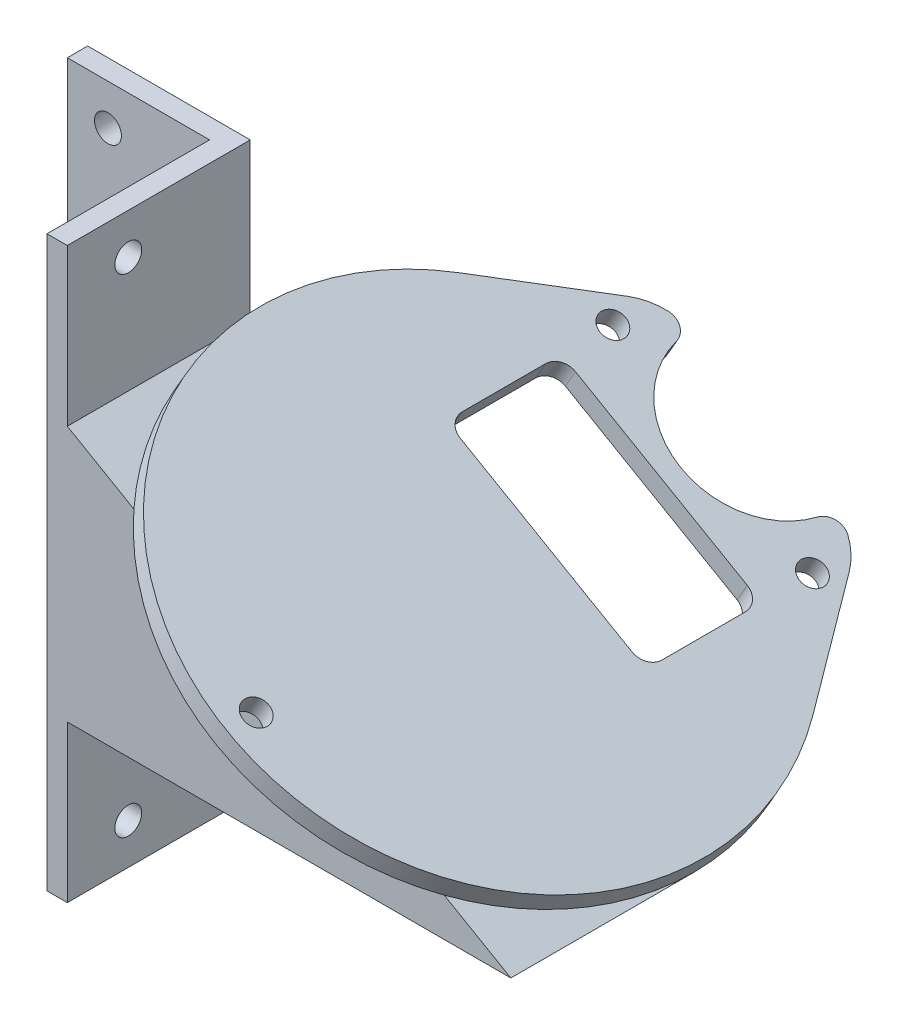
SolidWorks part; units mm, degrees
ref_plane "Front Plane" through (0, 0, 0) normal (0, 0, 1) x (1, 0, 0)
ref_plane "Top Plane" through (0, 0, 0) normal (0, 1, 0) x (1, 0, 0)
ref_plane "Right Plane" through (0, 0, 0) normal (1, 0, 0) x (0, 0, -1)
sketch "Sketch2" plane through (0, 0, 0) normal (1, 0, 0) x (0, 0, -1)
  line L0 (0, 0) -> (26.9799, 0) construction
ref_plane "Plane1" through (0, 0, 0) normal (0.5, 0.866, 0) x (0, 0, -1)
sketch "Sketch3" plane through (0, 0, 0) normal (0.5, 0.866, 0) x (0, 0, -1)
  line L0 (36, 18) -> (36, -18) construction
  line L1 (-200000, 0) -> (200026.9799, 0) construction
  line L2 (24, 32) -> (40, 20)
  line L3 (44, 12) -> (44, -12) construction
  line L4 (40, -20) -> (24, -32)
  line L6 (10, 18) -> (28, 18)
  line L7 (10, 18) -> (10, -18)
  line L8 (10, -18) -> (28, -18)
  line L9 (28, 18) -> (28, -18)
  circle A0 centre (0, 0) radius 29.91 construction
  circle A1 centre (-35.3, 0) radius 2
  circle A2 centre (36, 18) radius 2
  circle A3 centre (36, -18) radius 2
  circle A4 centre (44, 0) radius 13 construction
  arc A5 (24, 32) -> (24, -32) centre (0, 0) ccw
  arc A6 (44, -12) -> (40, -20) centre (34, -12) cw
  arc A7 (40, 20) -> (44, 12) centre (34, 12) cw
  circle A8 centre (44, 0) radius 13
  point P9 (36, 0)
  point P10 (44, 0)
  point P25 (44, 17)
  point P29 (10, 0)
  point P30 (10, 0)
  point P31 (0, -40)
  dimension "D1" = 59.82
  dimension "D2" = 4
  dimension "D7" = 26
  dimension "D8" = 40
  dimension "D10" = 10
  dimension "D3" = 35.3
  dimension "D4" = 36
  dimension "D5" = 36
  dimension "D6" = 44
  dimension "D9" = 25
  dimension "D11" = 10
  dimension "D12" = 18
  dimension "D13" = 36
extrude "Boss-Extrude1" add sketch "Sketch3" along normal blind 3.175 contours A8 A7 L2 A5 L4 A6 L6 L9 L8 L7 A1 A2 A3
fillet "Fillet1" radius 2.5 6 edges at (16.3822, -7.6252, -10) (16.3822, -7.6252, -28) (-14.7947, 10.3748, -28) (-14.7947, 10.3748, -10) (-10.4645, 7.8748, -43.9499) (12.052, -5.1251, -43.9499)
ref_plane "Plane2" through (0, -20, 0) normal (0, 1, 0) x (1, 0, 0)
sketch "Sketch4" plane through (0, -20, 0) normal (0, 1, 0) x (1, 0, 0)
  line L0 (18.766, 44.45) -> (18.766, -44.45) construction
  line L1 (34.641, 44.45) -> (2.891, 44.45)
  line L2 (34.641, 44.45) -> (34.641, -44.45)
  line L3 (34.641, -44.45) -> (2.891, -44.45)
  line L4 (2.891, 44.45) -> (2.891, -44.45)
  line L5 (18.766, 38.1) -> (18.766, -38.1) construction
  circle A0 centre (18.766, 38.1) radius 2.25
  circle A1 centre (18.766, -38.1) radius 2.25
  dimension "D2" = 4.5
  dimension "D1" = 31.75
  dimension "D3" = 76.2
  dimension "D4" = 38.1
  dimension "D5" = 88.9
sketch "Sketch6" plane through (0, 0, 0) normal (0, 0, 1) x (1, 0, 0)
  line L1 (-34.641, 44.45) -> (-60.041, 44.45)
  line L2 (-34.641, 44.45) -> (-34.641, -44.45)
  line L3 (-34.641, -44.45) -> (-60.041, -44.45)
  line L4 (-60.041, 44.45) -> (-60.041, -44.45)
  line L15 (-34.641, 20) -> (34.641, -20) construction
  line L16 (15.5885, -9) -> (-34.641, -9)
  line L17 (-34.641, 20) -> (34.641, -20)
  line L18 (0, 0) -> (-34.641, 0) construction
  point P5 (0, 0)
  point P6 (0, 0)
  dimension "D1" = 88.9
  dimension "D2" = 25.4
extrude "Boss-Extrude2" add sketch "Sketch6" along normal blind 3.175 contours L18 L17 L2
sketch "Sketch7" plane through (0, 0, 0) normal (0, 0, -1) x (-1, 0, 0)
  line L1 (34.641, -44.45) -> (37.816, -44.45)
  line L2 (34.641, -44.45) -> (34.641, 44.45)
  line L3 (34.641, 44.45) -> (37.816, 44.45)
  line L4 (37.816, -44.45) -> (37.816, 44.45)
  line L5 (34.641, 44.45) -> (60.041, 44.45) construction
  point P5 (37.816, 44.45)
  point P7 (0, 0)
  point P8 (0, 0)
  point P10 (0, 0)
  point P11 (0, 0)
  point P12 (34.641, -44.45)
  dimension "D1" = 3.175
extrude "Boss-Extrude3" add sketch "Sketch7" against normal blind 28.575
sketch "Sketch8" plane through (0, 0, 3.175) normal (0, 0, 1) x (1, 0, 0)
  line L0 (-37.816, -44.45) -> (-37.816, 44.45) construction
  line L4 (-37.816, 44.45) -> (-60.041, 44.45) construction
  circle A0 centre (-53.691, 38.1) radius 2.1
  circle A1 centre (-53.691, -38.1) radius 2.1
  point P6 (0, 0)
  point P7 (0, 0)
  dimension "D2" = 4.2
  dimension "D1" = 15.875
  dimension "D3" = 76.2
  dimension "D4" = 6.35
extrude "Cut-Extrude1" cut sketch "Sketch8" against normal blind 25.4
sketch "Sketch9" plane through (-37.816, 0, 0) normal (-1, 0, 0) x (0, 0, 1)
  line L0 (3.175, 36) -> (3.175, 40.2) construction
  line L1 (3.175, 36) -> (3.175, 40.2)
  circle A0 centre (19.05, 38.1) radius 2.1
  circle A1 centre (19.05, -38.1) radius 2.1
  point P2 (3.175, 38.1)
  point P5 (19.05, 40.2)
  point P6 (0, 0)
  point P7 (0, 0)
  dimension "D1" = 15.875
  dimension "D2" = 76.2
extrude "Cut-Extrude2" cut sketch "Sketch9" against normal blind 25.4 contours A0 | A1
sketch "Sketch10" plane through (0, 0, 3.175) normal (0, 0, 1) x (1, 0, 0)
  line L0 (34.641, -20) -> (-34.641, 20) construction
  line L1 (34.641, -20) -> (-34.641, 20)
  line L2 (34.641, -20) -> (-34.641, -20)
  line L3 (-34.641, -20) -> (-34.641, 0)
  line L4 (-34.641, 20) -> (-34.641, 0)
  line L5 (-34.641, 0) -> (0, 0)
  line L6 (0, 0) -> (-34.5317, 19.9369)
  line L7 (-34.5317, 19.9369) -> (-34.641, 20)
  line L8 (-34.641, 20) -> (-34.641, 0)
  line L9 (-34.641, 0) -> (0, 0)
  line L10 (0, 0) -> (-34.5317, 19.9369)
  line L11 (-34.5317, 19.9369) -> (-34.641, 20)
  line M5 (-34.641, 20) -> (-34.641, 0)
  line M6 (-34.641, 0) -> (0, 0)
  line M7 (0, 0) -> (-34.5317, 19.9369)
  line M8 (-34.5317, 19.9369) -> (-34.641, 20)
  dimension "D1" = 0
extrude "Boss-Extrude4" add sketch "Sketch10" along normal up to surface and the other way up to surface contours L3 L2 L1 M6 | M8 M5 M6 M7
